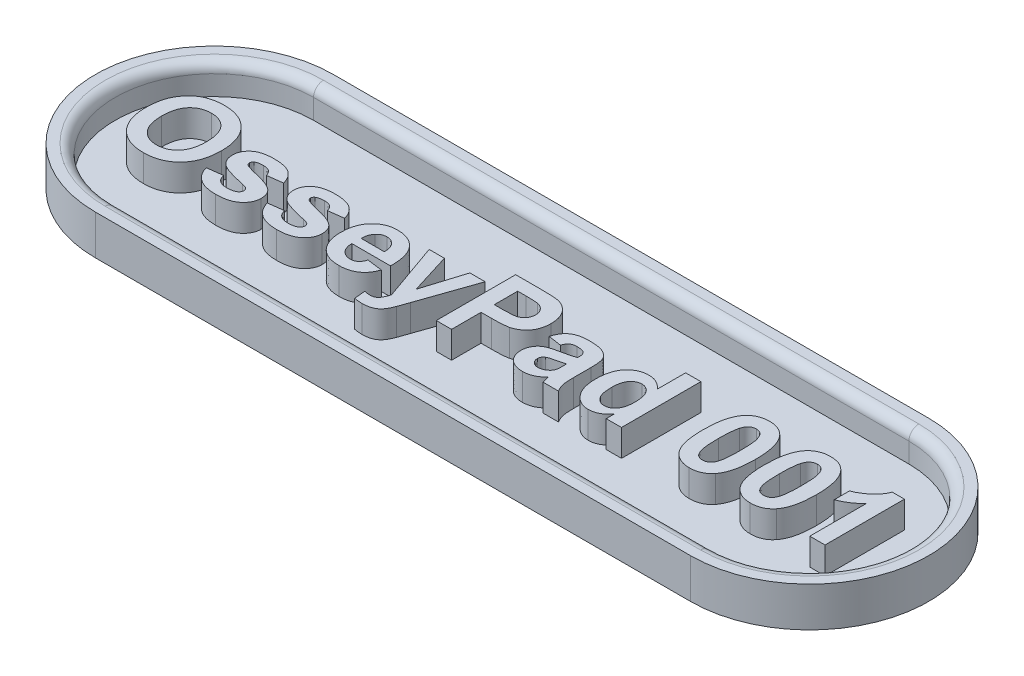
SolidWorks part; units mm, degrees
material "ABS PC"
ref_plane "Front Plane" through (0, 0, 0) normal (0, 0, 1) x (1, 0, 0)
ref_plane "Top Plane" through (0, 0, 0) normal (0, 1, 0) x (1, 0, 0)
ref_plane "Right Plane" through (0, 0, 0) normal (1, 0, 0) x (0, 0, -1)
sketch "Sketch1" plane through (0, 0, 0) normal (0, 1, 0) x (1, 0, 0)
  line L0 (-15, 0) -> (15, 0) construction
  line L1 (-15, 6) -> (15, 6)
  line L2 (-15, -6) -> (15, -6)
  arc A0 (-15, 6) -> (-15, -6) centre (-15, 0) ccw
  arc A1 (15, -6) -> (15, 6) centre (15, 0) ccw
  point P2 (0, 0)
  dimension "D1" = 12
  dimension "D2" = 30
extrude "Boss-Extrude1" add sketch "Sketch1" along normal blind 2
sketch "Sketch2" plane through (0, 2, 0) normal (0, 1, 0) x (1, 0, 0)
  line L0 (-15, 0) -> (15, 0) construction
  line L1 (-15, 5) -> (15, 5)
  line L2 (-15, -5) -> (15, -5)
  arc A0 (-15, 5) -> (-15, -5) centre (-15, 0) ccw
  arc A1 (15, -5) -> (15, 5) centre (15, 0) ccw
  point P2 (0, 0)
  dimension "D1" = 30
  dimension "D2" = 10
extrude "Cut-Extrude1" cut sketch "Sketch2" against normal blind 1.5
sketch "Sketch3" plane through (0, 0.5, 0) normal (0, 1, 0) x (1, 0, 0)
  line L0 (-21, -1.995) -> (21, -1.995) construction
  line L1 (0, -8.7006) -> (0, 6.9821) construction
  line L3 (-15, -5) -> (15, -5) construction
  text T0 "OsseyPad 001" font "Arial" height 4
  dimension "D1" = 3.005
extrude "Boss-Extrude2" add sketch "Sketch3" along normal blind 1.35
fillet "Fillet1" radius 0.5 4 edges at (0, 2, -5) (20, 2, 0) (0, 2, 5) (-20, 2, 0)
